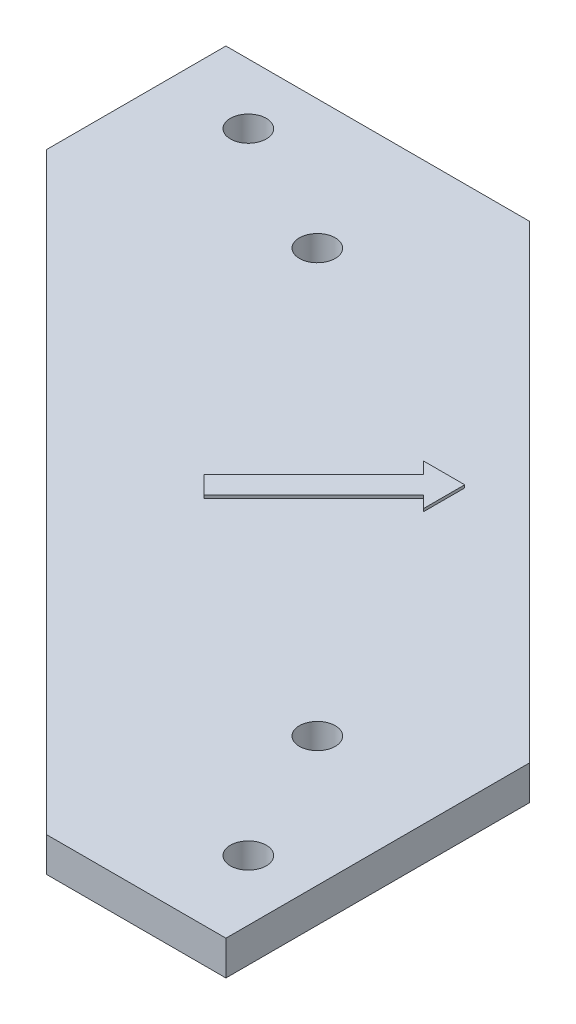
SolidWorks part; units mm, degrees
other "Markup2"
sketch "Sketch3" plane through (-71.12, 3.175, 71.12) normal (-0.1235, 0.7351, 0.6667) x (0.9905, 0.0505, 0.1278)
ref_plane "Front Plane" through (0, 0, 0) normal (0, 0, 1) x (1, 0, 0)
ref_plane "Top Plane" through (0, 0, 0) normal (0, 1, 0) x (1, 0, 0)
ref_plane "Right Plane" through (0, 0, 0) normal (1, 0, 0) x (0, 0, -1)
sketch "Sketch1" plane through (0, 0, 0) normal (0, 1, 0) x (1, 0, 0)
  line L0 (0, 0) -> (-50.8, 0) construction
  line L5 (-50.8, 0) -> (-63.5, 0) construction
  line L6 (-50.8, 0) -> (-50.8, -11.9058) construction
  line L7 (-63.5, 0) -> (-63.5, -5.5561) construction
  line L8 (0, 0) -> (0, -50.8) construction
  line L9 (0, -50.8) -> (0, -63.5) construction
  line L10 (0, -50.8) -> (-11.9058, -50.8) construction
  line L11 (0, -63.5) -> (-5.5561, -63.5) construction
  line L12 (-43.18, 0) -> (0, -43.18)
  line L13 (0, 0) -> (-71.12, 0)
  line L14 (0, 0) -> (0, -71.12)
  line L17 (-71.12, 0) -> (-71.12, -16.51)
  line L18 (-71.12, -16.51) -> (-16.51, -71.12)
  line L19 (0, -71.12) -> (-16.51, -71.12)
  circle A2 centre (-63.5, -5.5561) radius 1.651
  circle A3 centre (-50.8, -11.9058) radius 1.651
  circle A4 centre (-11.9058, -50.8) radius 1.651
  circle A5 centre (-5.5561, -63.5) radius 1.651
  dimension "D3" = 3.302
  dimension "D4" = 3.302
  dimension "D10" = 3.302
  dimension "D11" = 3.302
  dimension "D1" = 50.8
  dimension "D2" = 12.7
  dimension "D5" = 5.5561
  dimension "D6" = 11.9058
  dimension "D7" = 50.8
  dimension "D8" = 12.7
  dimension "D9" = 11.9058
  dimension "D12" = 5.5561
  dimension "D13" = 7.62
  dimension "D14" = 7.62
  dimension "D15" = 16.51
  dimension "D16" = 16.51
  dimension "D17" = 7.62
  dimension "D18" = 7.62
extrude "Boss-Extrude2" add sketch "Sketch1" along normal blind 3.175
sketch "Sketch5" plane through (0, 3.175, 0) normal (0, 1, 0) x (1, 0, 0)
  line L0 (-21.59, -21.59) -> (-24.8994, -24.239) construction
  line L1 (-24.8994, -24.239) -> (-28.7094, -24.239)
  line L2 (-24.8994, -24.239) -> (-24.8994, -28.049)
  line L5 (-43.18, 0) -> (0, -43.18) construction
  line L6 (-28.7094, -24.239) -> (-27.6318, -25.3167)
  line L7 (-24.8994, -28.049) -> (-25.9771, -26.9714)
  line L9 (-27.6318, -25.3167) -> (-37.7271, -35.412)
  line L10 (-25.9771, -26.9714) -> (-36.0724, -37.0667)
  line L11 (-37.7271, -35.412) -> (-36.0724, -37.0667)
extrude "Boss-Extrude3" add sketch "Sketch5" along normal blind 0.254
equation "\"D15\"=0.65"
